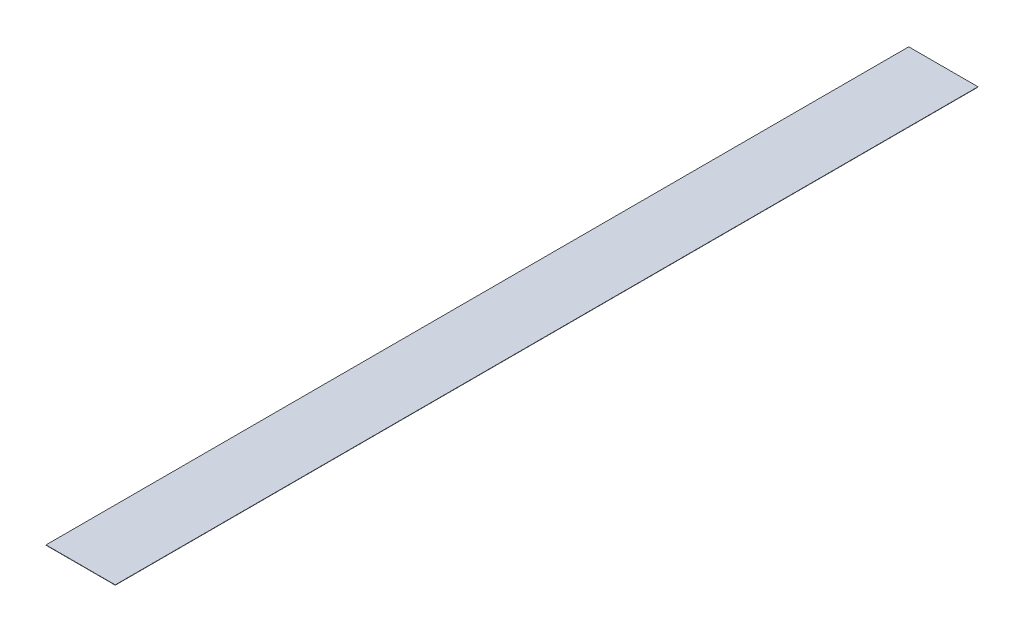
SolidWorks part; units mm, degrees
material "cable mix no adhesive"
ref_plane "Front" through (0, 0, 0) normal (0, 0, 1) x (1, 0, 0)
ref_plane "Top" through (0, 0, 0) normal (0, 1, 0) x (1, 0, 0)
ref_plane "Right" through (0, 0, 0) normal (1, 0, 0) x (0, 0, -1)
sketch "Sketch1" plane through (0, 0, 0) normal (0, 1, 0) x (1, 0, 0)
  line L0 (12.3027, 153.25) -> (-12.3027, -153.25) construction
  line L1 (-12.3027, 153.25) -> (12.3027, 153.25)
  line L2 (-12.3027, 153.25) -> (-12.3027, -153.25)
  line L3 (-12.3027, -153.25) -> (12.3027, -153.25)
  line L4 (12.3027, 153.25) -> (12.3027, -153.25)
  point P5 (0, 0)
  dimension "D1" = 24.6054
  dimension "D2" = 306.5
extrude "Extrude1" add sketch "Sketch1" along normal blind 0.1
